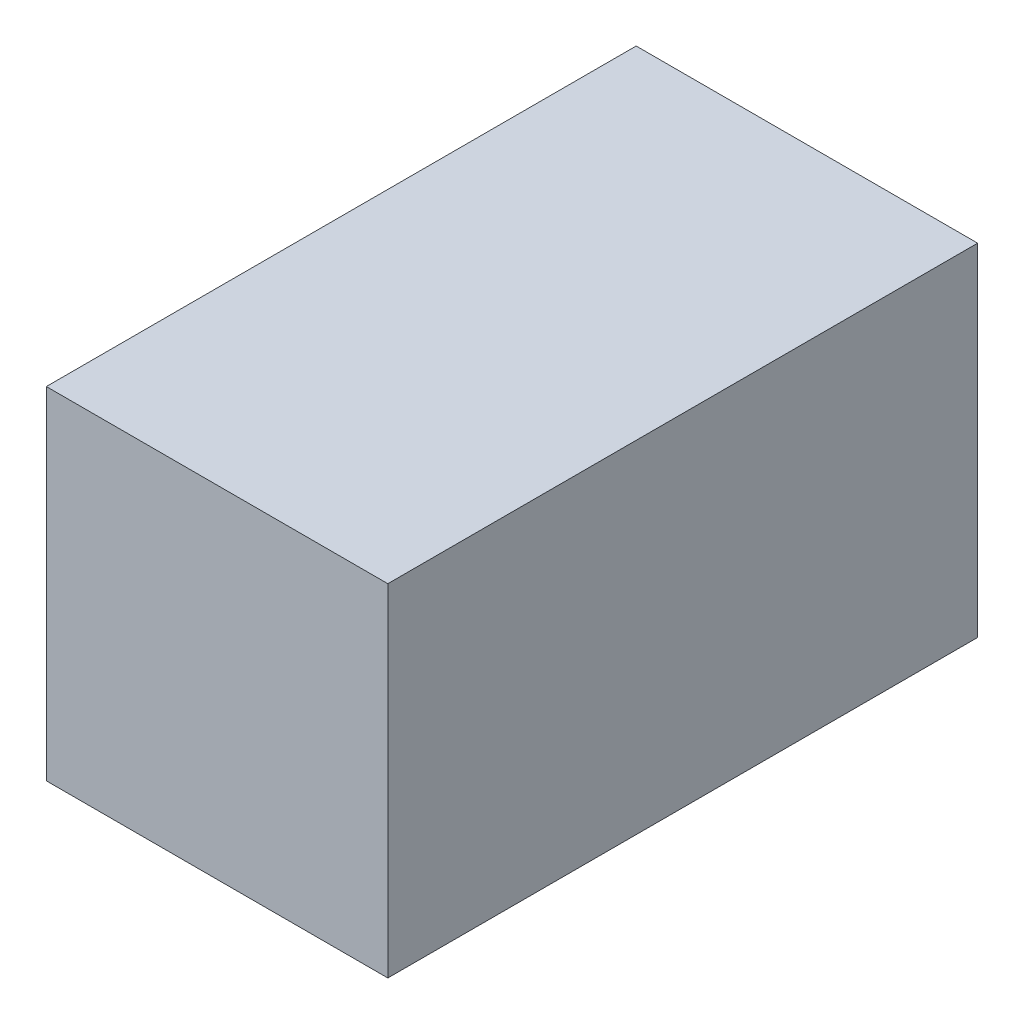
SolidWorks part; units mm, degrees
ref_plane "Plan de face" through (0, 0, 0) normal (0, 0, 1) x (1, 0, 0)
ref_plane "Plan de dessus" through (0, 0, 0) normal (0, 1, 0) x (1, 0, 0)
ref_plane "Plan de droite" through (0, 0, 0) normal (1, 0, 0) x (0, 0, -1)
sketch "Esquisse1" plane through (0, 0, 0) normal (0, 0, 1) x (1, 0, 0)
  line L1 (-27.5, -27.5) -> (27.5, -27.5)
  line L2 (-27.5, -27.5) -> (-27.5, 27.5)
  line L3 (-27.5, 27.5) -> (27.5, 27.5)
  line L4 (27.5, -27.5) -> (27.5, 27.5)
  line L5 (-27.5, -27.5) -> (27.5, 27.5) construction
  line L6 (-27.5, 27.5) -> (27.5, -27.5) construction
  point P0 (0, 0)
extrude "Boss.-Extru.2" add sketch "Esquisse1" along normal blind 95 contours L3 L4 L1 L2
